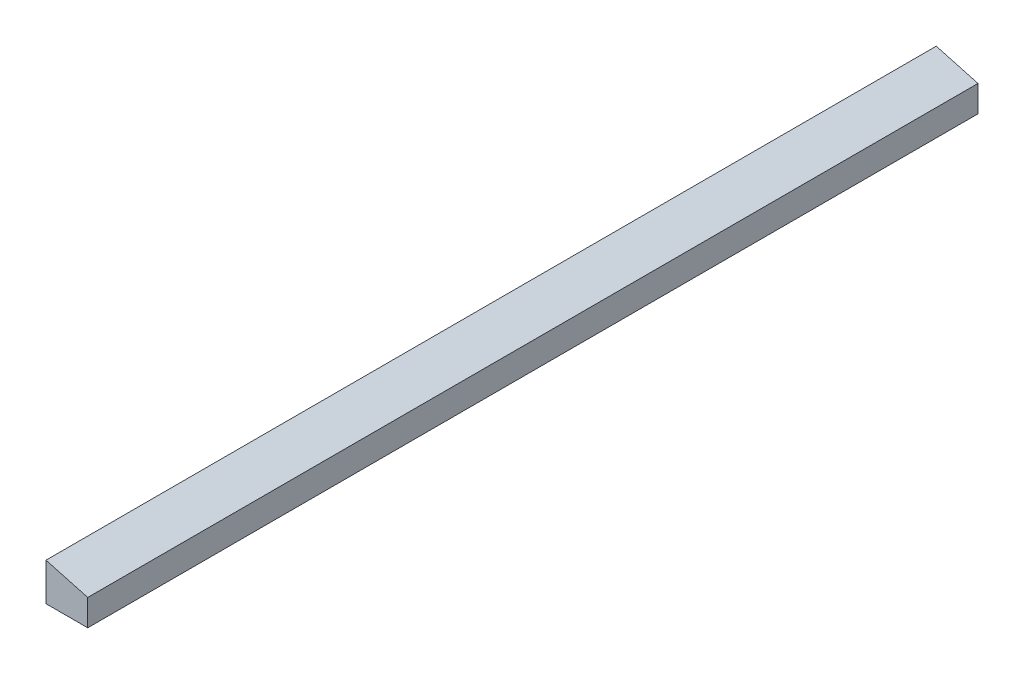
SolidWorks part; units mm, degrees
ref_plane "Front Plane" through (0, 0, 0) normal (0, 0, 1) x (1, 0, 0)
ref_plane "Top Plane" through (0, 0, 0) normal (0, 1, 0) x (1, 0, 0)
ref_plane "Right Plane" through (0, 0, 0) normal (1, 0, 0) x (0, 0, -1)
sketch "Sketch1" plane through (0, 0, 0) normal (0, 0, 1) x (1, 0, 0)
  line L0 (0, 6.35) -> (0, 32.2001)
  line L1 (0, 0) -> (88.9, 0)
  line L2 (0, 0) -> (0, 6.35)
  line L3 (0, 6.35) -> (88.9, 6.35)
  line L4 (88.9, 0) -> (88.9, 6.35)
  line L5 (0, 32.2001) -> (28.575, 24.3829)
  line L6 (28.575, 24.3829) -> (28.575, 6.35)
  line L7 (28.575, 6.35) -> (0, 6.35)
  line L8 (0, 32.2001) -> (3.3512, 44.45)
  line L9 (3.3512, 44.45) -> (154.6385, 3.0625)
  line L10 (154.6385, 3.0625) -> (153.8007, 0)
  line L11 (153.8007, 0) -> (117.7038, 0)
  line L12 (117.7038, 0) -> (0, 32.2001)
  line L13 (0, 45.3668) -> (0.8378, 48.4293)
  line L14 (0, 45.3668) -> (165.833, 0)
  line L15 (0.8378, 48.4293) -> (166.6708, 3.0625)
  line L16 (165.833, 0) -> (166.6708, 3.0625)
  dimension "D1" = 12.7
  dimension "D2" = 3.175
  dimension "D3" = 15.3
  dimension "D4" = 44.45
  dimension "D5" = 6.35
  dimension "D6" = 88.9
  dimension "D7" = 28.575
  dimension "D8" = 25.8501
  dimension "D9" = 156.8464
  dimension "D10" = 3.175
  dimension "D11" = 165.833
  dimension "D12" = 171.9265
extrude "Boss-Extrude1" add sketch "Sketch1" along normal mid plane 609.6 contours L6 L5 L0 L3
